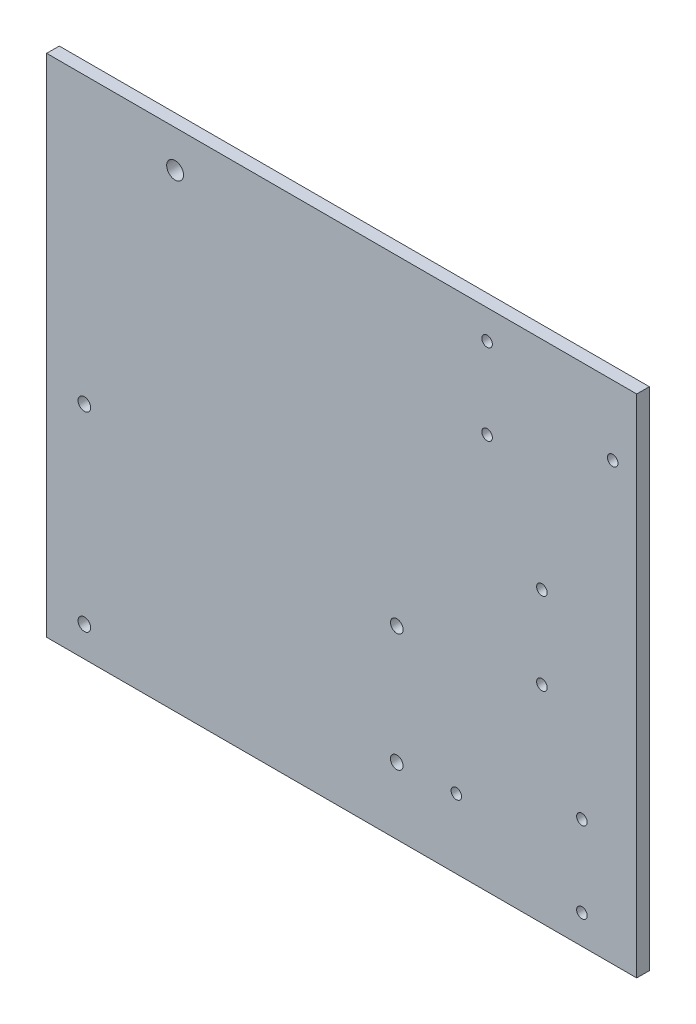
SolidWorks part; units mm, degrees
ref_plane "Front Plane" through (0, 0, 0) normal (0, 0, 1) x (1, 0, 0)
ref_plane "Top Plane" through (0, 0, 0) normal (0, 1, 0) x (1, 0, 0)
ref_plane "Right Plane" through (0, 0, 0) normal (1, 0, 0) x (0, 0, -1)
sketch "Sketch1" plane through (0, 0, 0) normal (0, 0, 1) x (1, 0, 0)
  line L1 (0, 0) -> (-140, 0)
  line L2 (0, 0) -> (0, 120)
  line L3 (0, 120) -> (-140, 120)
  line L4 (-140, 0) -> (-140, 120)
  circle A0 centre (-109.523, 111.2051) radius 2
  circle A4 centre (-131.05, 7.17) radius 1.5
  circle A5 centre (-131.05, 52.41) radius 1.5
  circle A6 centre (-56.93, 15.86) radius 1.5
  circle A7 centre (-56.93, 43.86) radius 1.5
  circle A9 centre (-13, 6.91) radius 1.25
  circle A10 centre (-13, 26.11) radius 1.25
  circle A11 centre (-42.8, 16.5) radius 1.25
  circle A15 centre (-35.5, 93.89) radius 1.25
  circle A16 centre (-35.5, 113.09) radius 1.25
  circle A17 centre (-5.7, 103.5) radius 1.25
  circle A18 centre (-22.5, 68.5276) radius 1.25
  circle A19 centre (-22.5, 49.0276) radius 1.25
  point P11 (-35.5, 71.4)
  point P30 (-22.5, 52.41)
  dimension "D3" = 4
  dimension "D6" = 8.95
  dimension "D7" = 45.24
  dimension "D8" = 8.95
  dimension "D9" = 3
  dimension "D10" = 2.5
  dimension "D11" = 56.93
  dimension "D4" = 3
  dimension "D5" = 7.17
  dimension "D12" = 3
  dimension "D13" = 3
  dimension "D14" = 19.2
  dimension "D16" = 2.5
  dimension "D17" = 6.91
  dimension "D18" = 13
  dimension "D19" = 2.5
  dimension "D20" = 13
  dimension "D21" = 19.2
  dimension "D22" = 29.8
  dimension "D23" = 2.5
  dimension "D24" = 16.5
  dimension "D26" = 6.91
  dimension "D25" = 2.5
  dimension "D27" = 16.5
  dimension "D28" = 35.5
  dimension "D29" = 35.5
  dimension "D30" = 29.8
  dimension "D31" = 2.5
  dimension "D32" = 28.5
  dimension "D33" = 22.5
  dimension "D34" = 2.5
  dimension "D1" = 120
  dimension "D2" = 140
  dimension "D15" = 56.93
  dimension "D35" = 19.5
extrude "Boss-Extrude1" add sketch "Sketch1" along normal blind 3
